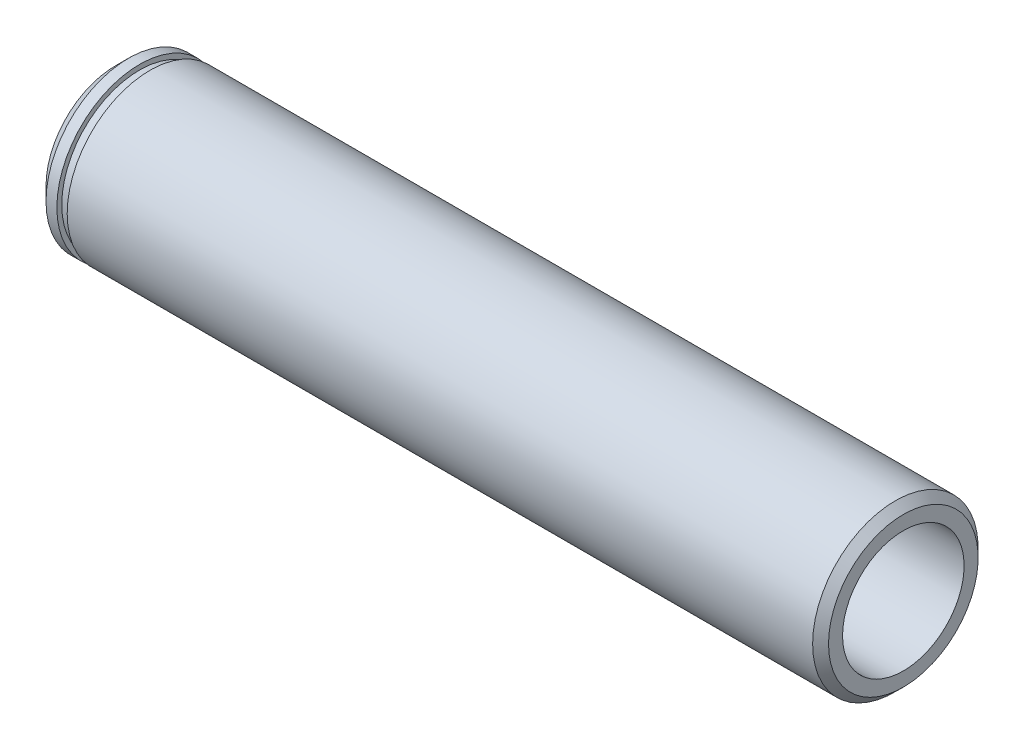
SolidWorks part; units mm, degrees
ref_plane "Front" through (0, 0, 0) normal (0, 0, 1) x (1, 0, 0)
ref_plane "Top" through (0, 0, 0) normal (0, 1, 0) x (1, 0, 0)
ref_plane "Right" through (0, 0, 0) normal (1, 0, 0) x (0, 0, -1)
ref_plane "Plane1" through (0, 0, 0) normal (0, 0, -1) x (-1, 0, 0)
sketch "Sketch1" plane through (0, 0, 0) normal (0, 0, -1) x (-1, 0, 0)
  line L0 (0, 5.9944) -> (0, 6.6675)
  line L1 (0, 6.6675) -> (-1.27, 7.9375)
  line L2 (-1.27, 7.9375) -> (-2.3114, 7.9375)
  line L3 (-2.3114, 7.9375) -> (-2.3114, 7.4676)
  line L4 (-2.3114, 7.4676) -> (-3.302, 7.4676)
  line L5 (-3.302, 7.4676) -> (-3.302, 7.9375)
  line L6 (-3.302, 7.9375) -> (-74.803, 7.9375)
  line L7 (-74.803, 7.9375) -> (-75.565, 7.1755)
  line L8 (-75.565, 7.1755) -> (-75.565, 5.8293)
  line L9 (-75.565, 5.8293) -> (-8.89, 5.8293)
  line L10 (-8.89, 5.8293) -> (-8.89, 5.9944)
  line L11 (-8.89, 5.9944) -> (0, 5.9944)
  line L12 (-75.565, 0) -> (0, 0) construction
revolve "Revolve1" add sketch "Sketch1" angle 360 about L12
